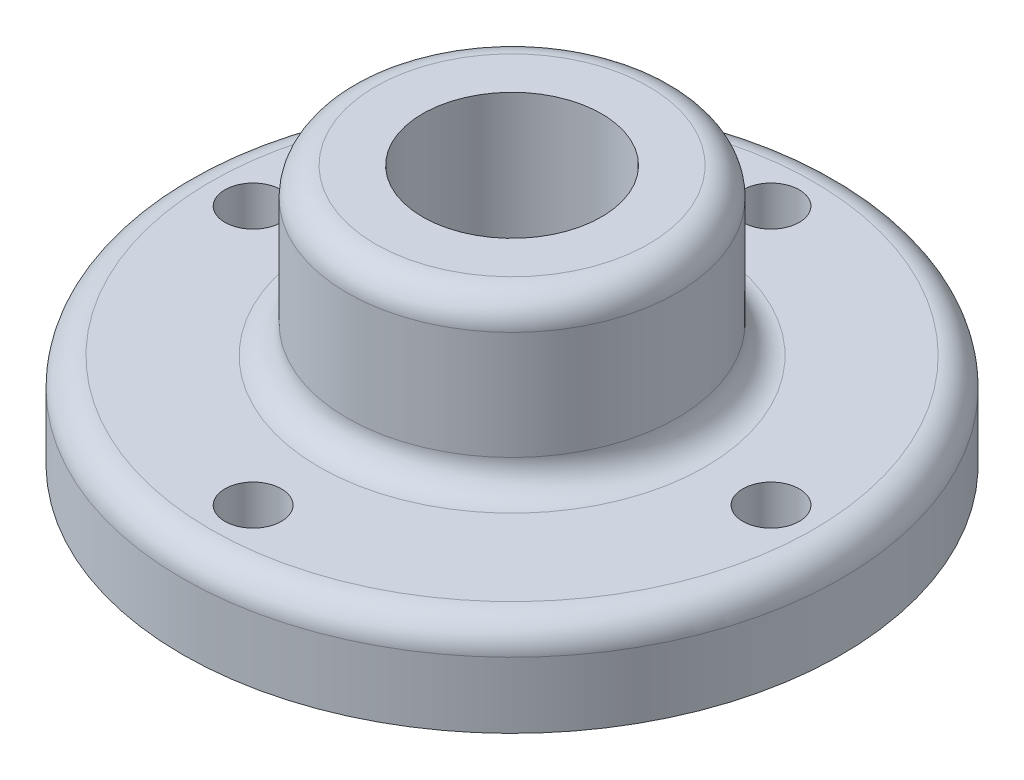
SolidWorks part; units mm, degrees
ref_plane "Front Plane" through (0, 0, 0) normal (0, 0, 1) x (1, 0, 0)
ref_plane "Top Plane" through (0, 0, 0) normal (0, 1, 0) x (1, 0, 0)
ref_plane "Right Plane" through (0, 0, 0) normal (1, 0, 0) x (0, 0, -1)
sketch "Sketch1" plane through (0, 0, 0) normal (0, 1, 0) x (1, 0, 0)
  circle A0 centre (0, 0) radius 70
  circle A1 centre (0, 0) radius 55
  circle A2 centre (0, 55) radius 6
  circle A3 centre (55, 0) radius 6
  circle A4 centre (0, -55) radius 6
  circle A5 centre (-55, 0) radius 6
  dimension "D1" = 140
  dimension "D2" = 12
  dimension "D3" = 12
  dimension "D4" = 110
  dimension "D5" = 12
  dimension "D6" = 12
extrude "Boss-Extrude1" add sketch "Sketch1" along normal blind 20 contours A5 A1 A4 A3 A2 | A0 A5 A1 A2 A3 A4
sketch "Sketch2" plane through (0, 20, 0) normal (0, 1, 0) x (1, 0, 0)
  circle A0 centre (0, 0) radius 35
  dimension "D1" = 70
extrude "Boss-Extrude2" add sketch "Sketch2" along normal blind 35
sketch "Sketch3" plane through (0, 55, 0) normal (0, 1, 0) x (1, 0, 0)
  circle A0 centre (0, 0) radius 19
  dimension "D1" = 38
extrude "Cut-Extrude1" cut sketch "Sketch3" against normal through all
fillet "Fillet1" radius 6 3 edges at (0, 20, 70) (0, 20, 35) (0, 55, 35)
equation "\"D1@Boss-Extrude2\"=55-20"
